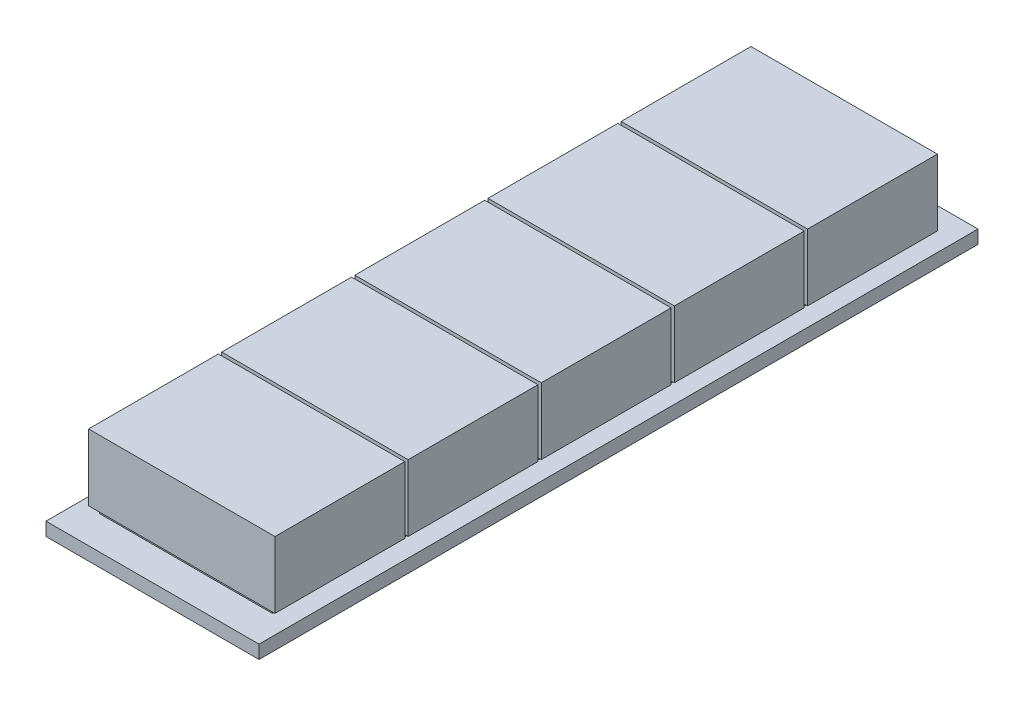
SolidWorks part; units mm, degrees
ref_plane "Front Plane" through (0, 0, 0) normal (0, 0, 1) x (1, 0, 0)
ref_plane "Top Plane" through (0, 0, 0) normal (0, 1, 0) x (1, 0, 0)
ref_plane "Right Plane" through (0, 0, 0) normal (1, 0, 0) x (0, 0, -1)
sketch "Sketch1" plane through (0, 0, 0) normal (0, 1, 0) x (1, 0, 0)
  line L1 (-40, -135) -> (40, -135)
  line L2 (-40, -135) -> (-40, 135)
  line L3 (-40, 135) -> (40, 135)
  line L4 (40, -135) -> (40, 135)
  line L5 (-40, -135) -> (40, 135) construction
  line L6 (-40, 135) -> (40, -135) construction
  point P0 (0, 0)
  dimension "D1" = 80
  dimension "D2" = 270
extrude "Boss-Extrude1" add sketch "Sketch1" along normal blind 5
sketch "Sketch2" plane through (0, 5, 0) normal (0, 1, 0) x (1, 0, 0)
  line L0 (0, 0) -> (0, -135) construction
  line L1 (-40, -135) -> (40, -135) construction
  line L3 (-32.5, -77.5) -> (32.5, -77.5)
  line L4 (-32.5, -77.5) -> (-32.5, -122.5)
  line L5 (-32.5, -122.5) -> (32.5, -122.5)
  line L6 (32.5, -77.5) -> (32.5, -122.5)
  line L7 (-32.5, -77.5) -> (32.5, -122.5) construction
  line L8 (-32.5, -122.5) -> (32.5, -77.5) construction
  point P5 (0, -100)
  dimension "D1" = 65
  dimension "D2" = 45
  dimension "D3" = 12.5
extrude "Boss-Extrude3" add sketch "Sketch2" along normal blind 2
pattern_linear "LPattern1" count 5 spacing 50 along (0, 0, -1) of "Boss-Extrude3"
sketch "Sketch3" plane through (0, 7, 0) normal (0, 1, 0) x (1, 0, 0)
  line L0 (0, 0) -> (0, -122.5) construction
  line L1 (-32.5, -122.5) -> (32.5, -122.5) construction
  line L2 (-40, 135) -> (-40, -135) construction
  line L3 (-35, -75.2605) -> (35, -75.2605)
  line L4 (-35, -75.2605) -> (-35, -124.0095)
  line L5 (-35, -124.0095) -> (35, -124.0095)
  line L6 (35, -75.2605) -> (35, -124.0095)
  line L7 (-35, -75.2605) -> (35, -124.0095) construction
  line L8 (-35, -124.0095) -> (35, -75.2605) construction
  point P5 (0, -99.635)
  dimension "D1" = 5
extrude "Boss-Extrude8" add sketch "Sketch3" along normal blind 25
pattern_linear "LPattern5" count 5 spacing 50 along (0, 0, -1) of "Boss-Extrude8"
